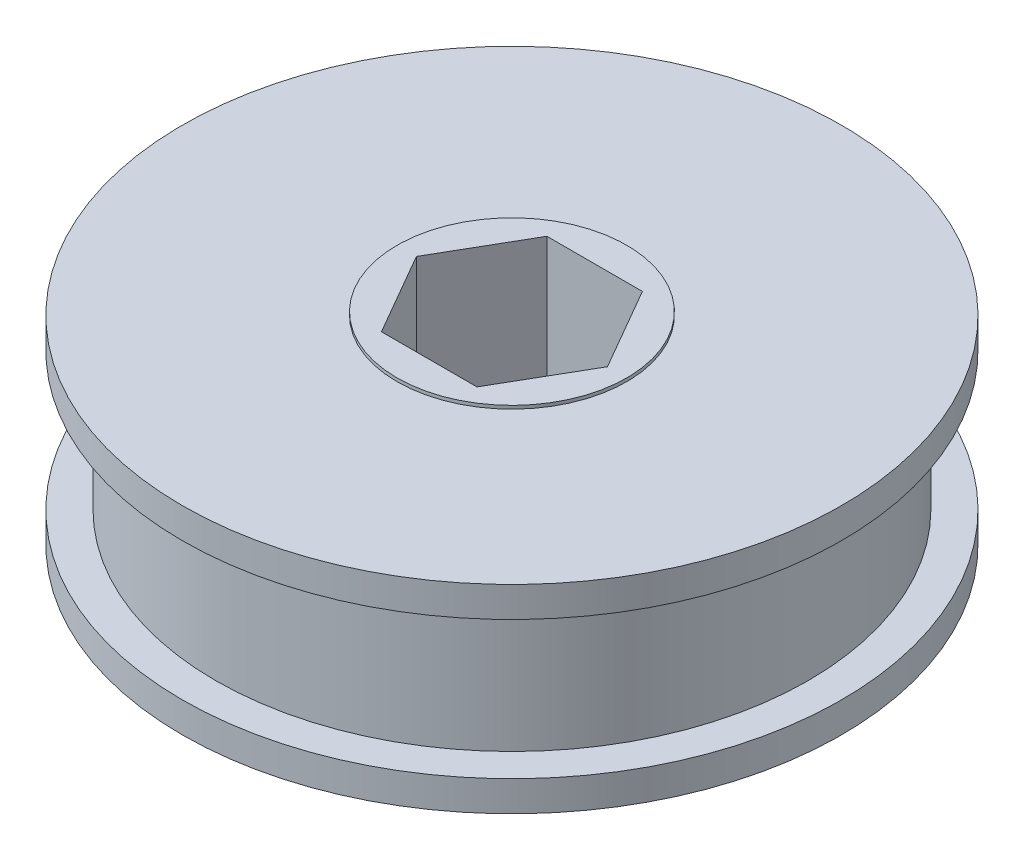
SolidWorks part; units mm, degrees
ref_plane "Front Plane" through (0, 0, 0) normal (0, 0, 1) x (1, 0, 0)
ref_plane "Top Plane" through (0, 0, 0) normal (0, 1, 0) x (1, 0, 0)
ref_plane "Right Plane" through (0, 0, 0) normal (1, 0, 0) x (0, 0, -1)
ref_axis "Axis1" through (0, 55, 0) along (0, -1, 0)
sketch "Sketch2" plane through (0, 0, 0) normal (1, 0, 0) x (0, 0, -1)
  line L0 (2.54, -3.2131) -> (8.89, -3.2131)
  line L1 (8.89, -3.2131) -> (8.89, -3.4671)
  line L2 (8.89, -3.4671) -> (25.5016, -3.4671)
  line L3 (25.5016, -3.4671) -> (25.5016, -5.8166)
  line L5 (22.9235, -5.8166) -> (22.9235, -16.4846)
  line L7 (25.5016, -16.4846) -> (25.5016, -18.8341)
  line L8 (25.5016, -18.8341) -> (8.89, -18.8341)
  line L9 (8.89, -18.8341) -> (8.89, -19.0881)
  line L10 (8.89, -19.0881) -> (2.54, -19.0881)
  line L11 (22.9235, -5.8166) -> (25.5016, -5.8166)
  line L13 (2.54, -19.0881) -> (2.54, -3.2131)
  line L14 (0, 55) -> (0, -55) construction
  line L17 (22.9235, -16.4846) -> (25.5016, -16.4846)
  dimension "D1" = 15.875
  dimension "D2" = 2.54
  dimension "D3" = 25.5016
  dimension "D4" = 6.35
  dimension "D5" = 0.254
  dimension "D6" = 10.668
  dimension "D7" = 22.9235
revolve "Revolve1" add sketch "Sketch2" angle 360 about axis through (0, 55, 0) along (0, -1, 0)
sketch "Sketch3" plane through (0, -3.2131, 0) normal (0, 1, 0) x (1, 0, 0)
  line L1 (3.6955, 6.4008) -> (-3.6955, 6.4008)
  line L2 (-3.6955, 6.4008) -> (-7.391, 0)
  line L3 (-7.391, 0) -> (-3.6955, -6.4008)
  line L4 (-3.6955, -6.4008) -> (3.6955, -6.4008)
  line L5 (3.6955, -6.4008) -> (7.391, 0)
  line L6 (7.391, 0) -> (3.6955, 6.4008)
  circle A0 centre (0, 0) radius 6.4008 construction
  dimension "D1" = 12.8016
extrude "Cut-Extrude1" cut sketch "Sketch3" against normal through all both and the other way through all
